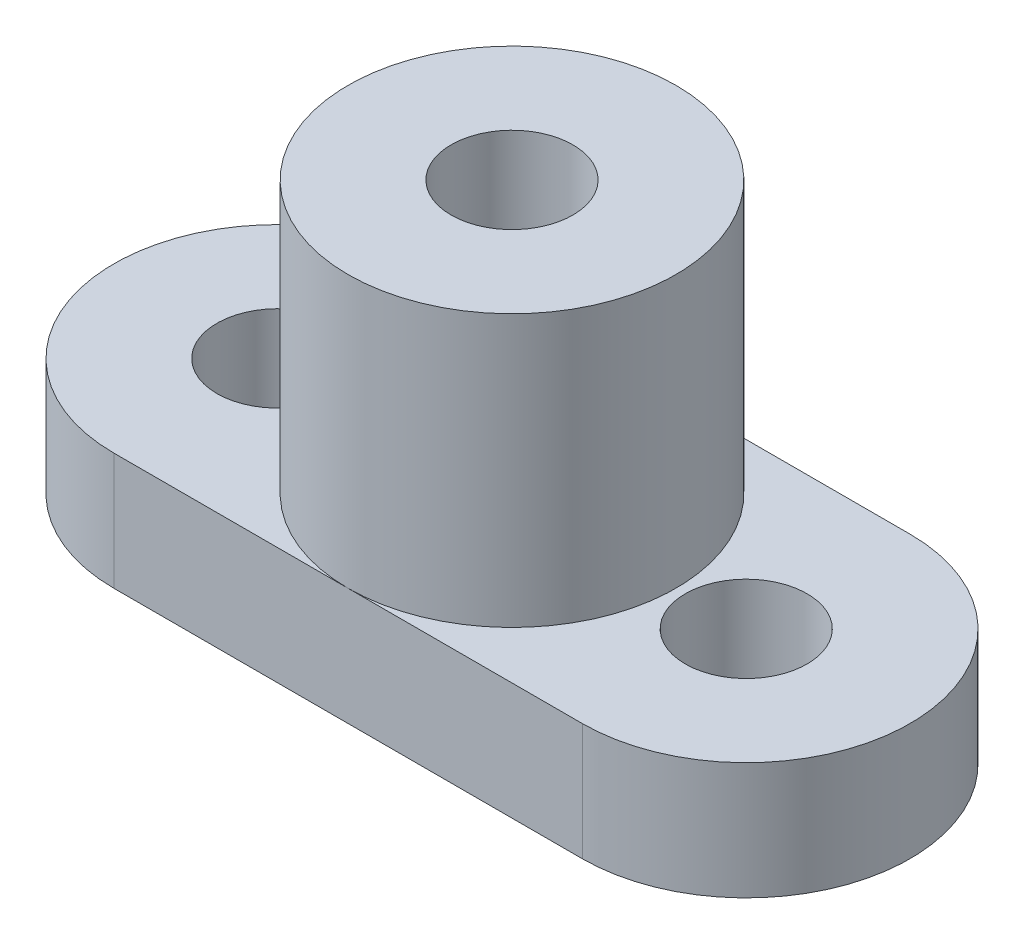
SolidWorks part; units mm, degrees
ref_plane "Front Plane" through (0, 0, 0) normal (0, 0, 1) x (1, 0, 0)
ref_plane "Top Plane" through (0, 0, 0) normal (0, 1, 0) x (1, 0, 0)
ref_plane "Right Plane" through (0, 0, 0) normal (1, 0, 0) x (0, 0, -1)
sketch "Sketch1" plane through (0, 0, 0) normal (0, 1, 0) x (1, 0, 0)
  line L0 (0, 0) -> (12.7, 0) construction
  line L1 (0, 4.445) -> (12.7, 4.445)
  line L2 (0, -4.445) -> (12.7, -4.445)
  arc A0 (0, 4.445) -> (0, -4.445) centre (0, 0) ccw
  arc A1 (12.7, -4.445) -> (12.7, 4.445) centre (12.7, 0) ccw
  circle A2 centre (12.7, 0) radius 1.651
  circle A3 centre (0, 0) radius 1.651
  point P3 (6.35, 0)
  point P12 (18.1635, 0)
  point P13 (0, 0)
  point P14 (0, 0)
  dimension "D1" = 3.302
  dimension "D2" = 12.7
  dimension "D3" = 8.89
extrude "Boss-Extrude1" add sketch "Sketch1" along normal blind 3.175
sketch "Sketch2" plane through (0, 3.175, 0) normal (0, 1, 0) x (1, 0, 0)
  line L0 (0, -4.445) -> (12.7, -4.445) construction
  line L1 (12.7, 4.445) -> (0, 4.445) construction
  circle A0 centre (6.35, 0) radius 4.445
  circle A1 centre (6.35, 0) radius 1.651
  point P3 (6.35, -4.2508)
  point P8 (6.35, -4.445)
  dimension "D1" = 3.302
extrude "Boss-Extrude2" add sketch "Sketch2" along normal blind 7.366
